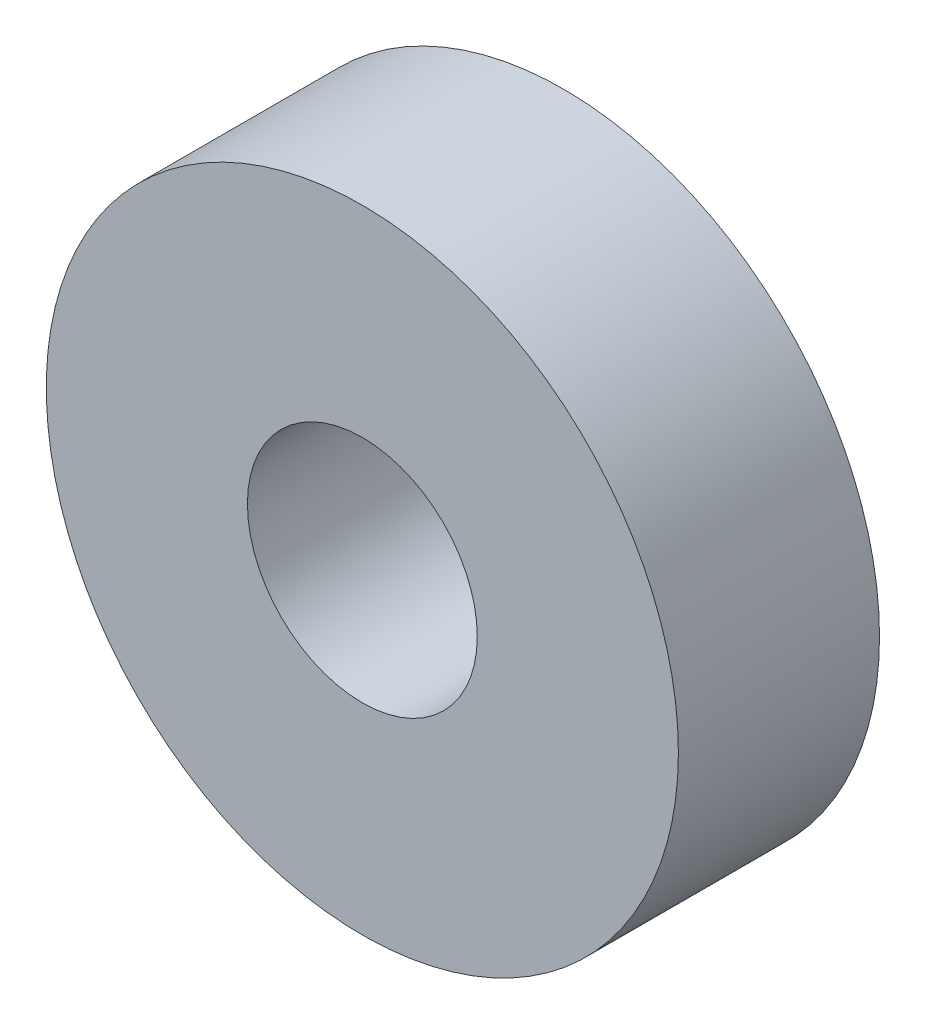
SolidWorks part; units mm, degrees
ref_plane "Plano frontal" through (0, 0, 0) normal (0, 0, 1) x (1, 0, 0)
ref_plane "Plano superior" through (0, 0, 0) normal (0, 1, 0) x (1, 0, 0)
ref_plane "Plano direito" through (0, 0, 0) normal (1, 0, 0) x (0, 0, -1)
sketch "Esboço1" plane through (0, 0, 0) normal (0, 0, 1) x (1, 0, 0)
  circle A0 centre (0, 0) radius 11
  dimension "D1" = 22
extrude "Ressalto-extrusão1" add sketch "Esboço1" along normal blind 7
sketch "Esboço2" plane through (0, 0, 7) normal (0, 0, 1) x (1, 0, 0)
  circle A0 centre (0, 0) radius 4
  dimension "D1" = 8
extrude "Corte-extrusão1" cut sketch "Esboço2" against normal through all both and the other way through all
